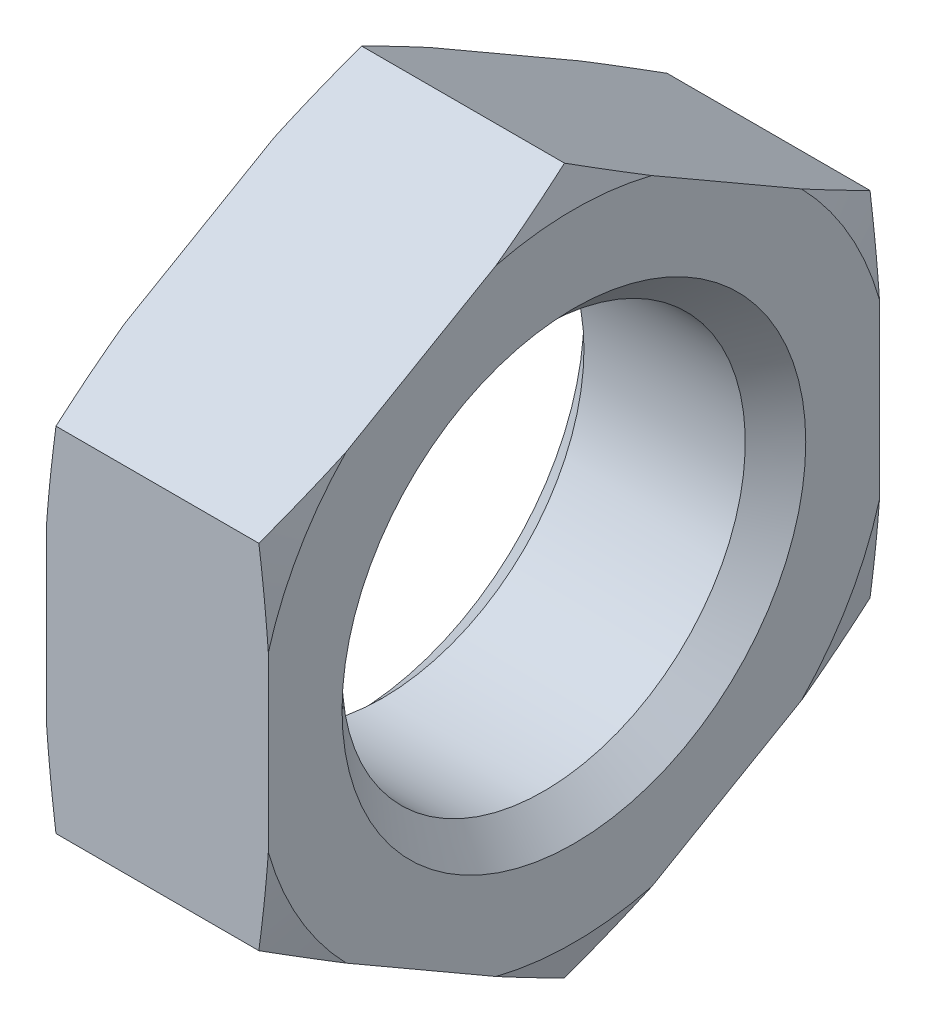
SolidWorks part; units mm, degrees
material "Сталь ШХ15 ГОСТ 801-78"
ref_plane "Plane1" through (0, 0, 0) normal (0, 0, 1) x (1, 0, 0)
ref_plane "Plane2" through (0, 0, 0) normal (0, 1, 0) x (1, 0, 0)
ref_plane "Plane3" through (0, 0, 0) normal (1, 0, 0) x (0, 0, -1)
sketch "Эскиз3" plane through (0, 0, 0) normal (0, 0, 1) x (1, 0, 0)
  line L1 (1.1, 2) -> (1.1, 3.15)
  line L2 (1.1, 3.15) -> (1.0062, 3.5)
  line L3 (1.0062, 3.5) -> (-1.0062, 3.5)
  line L4 (-1.0062, 3.5) -> (-1.1, 3.15)
  line L5 (-1.1, 3.15) -> (-1.1, 2)
  line L7 (-1.1, 2) -> (1.1, 2)
  line L8 (0, 0) -> (0, 3.1024) construction
  line L9 (-2.7853, 0) -> (3.9948, 0) construction
  dimension "D1" = 2.2
  dimension "D2" = 15
  dimension "D3" = 15
  dimension "D4" = 3.5
  dimension "D5" = 2
  dimension "D6" = 3.15
revolve "Повернуть1" add sketch "Эскиз3" angle 360 about L9
sketch "Эскиз5" plane through (0, 0, 0) normal (1, 0, 0) x (0, 0, -1)
  line L1 (0, 3.5) -> (-3.0311, 1.75)
  line L2 (-3.0311, 1.75) -> (-3.0311, -1.75)
  line L3 (-3.0311, -1.75) -> (0, -3.5)
  line L4 (0, -3.5) -> (3.0311, -1.75)
  line L5 (3.0311, -1.75) -> (3.0311, 1.75)
  line L6 (3.0311, 1.75) -> (0, 3.5)
  circle A0 centre (0, 0) radius 3.0311 construction
extrude "Вырез-Вытянуть6" cut sketch "Эскиз5" against normal mid plane 2.2 flip side to cut contours L2 L3 L4 L5 L6 L1
chamfer "Фаска4" distance 0.3 angle 45 2 edges at (1.1, 0, 2) (-1.1, 0, 2)
